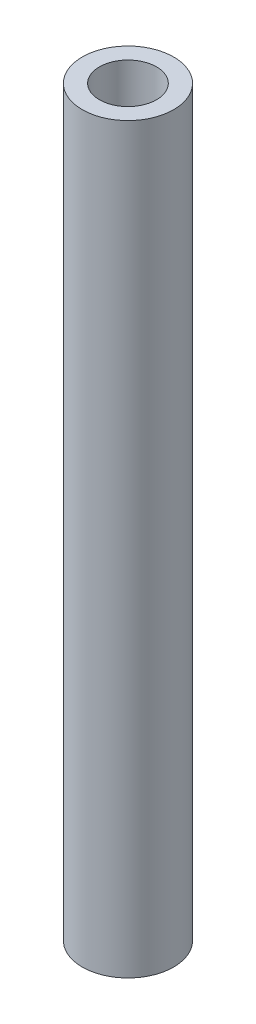
SolidWorks part; units mm, degrees
material "1060 Alloy"
ref_plane "Front Plane" through (0, 0, 0) normal (0, 0, 1) x (1, 0, 0)
ref_plane "Top Plane" through (0, 0, 0) normal (0, 1, 0) x (1, 0, 0)
ref_plane "Right Plane" through (0, 0, 0) normal (1, 0, 0) x (0, 0, -1)
sketch "Sketch1" plane through (0, 0, 0) normal (0, 1, 0) x (1, 0, 0)
  circle A0 centre (0, 0) radius 4
  circle A1 centre (0, 0) radius 2.5
  dimension "D1" = 8
  dimension "D2" = 5
extrude "Boss-Extrude1" add sketch "Sketch1" along normal blind 65
